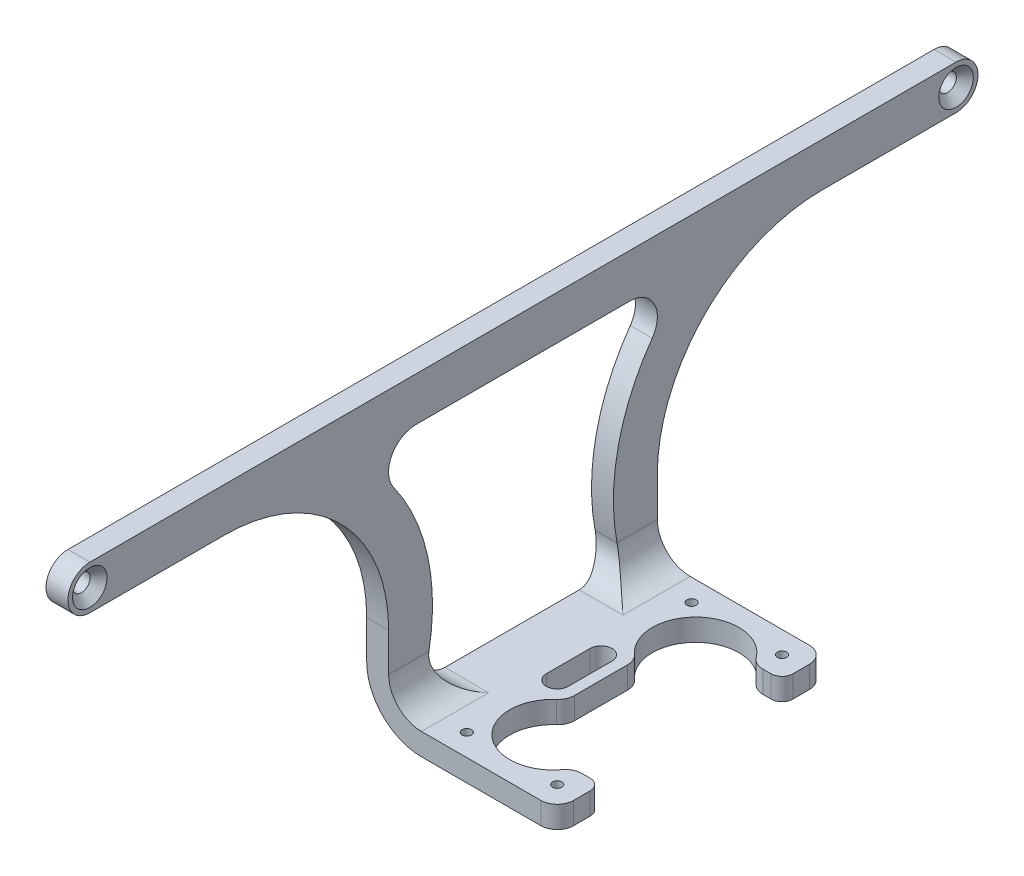
SolidWorks part; units mm, degrees
material "ABS"
ref_plane "Plan de face" through (0, 0, 0) normal (0, 0, 1) x (1, 0, 0)
ref_plane "Plan de dessus" through (0, 0, 0) normal (0, 1, 0) x (1, 0, 0)
ref_plane "Plan de droite" through (0, 0, 0) normal (1, 0, 0) x (0, 0, -1)
sketch "Esquisse1" plane through (0, 0, 0) normal (0, 0, 1) x (1, 0, 0)
  line L0 (0, 0) -> (-25, 0)
  line L1 (-35, 10) -> (-35, 55)
  line L2 (0, 4) -> (-25, 4)
  line L3 (-31, 10) -> (-31, 55)
  line L4 (0, 0) -> (0, 4)
  line L5 (-35, 55) -> (-31, 55)
  arc A2 (-25, 0) -> (-35, 10) centre (-25, 10) cw
  arc A3 (-25, 4) -> (-31, 10) centre (-25, 10) cw
  dimension "D1" = 10
  dimension "D3" = 55
  dimension "D4" = 25
  dimension "D2" = 4
extrude "Boss.-Extru.1" add sketch "Esquisse1" along normal blind 166
hole_wizard "Fraisage pour vis à tête fraisée M31" positions "Esquisse2" profile "Esquisse3" countersink size "M3" standard "ISO" end condition up to next
sketch "Esquisse2" plane through (-31, 0, 0) normal (-1, 0, 0) x (0, 0, 1)
  line L0 (0, 55) -> (0, 10) construction
  line L1 (166, 55) -> (0, 55) construction
  point P0 (4, 51)
  point P2 (162, 51)
  dimension "D1" = 158
  dimension "D2" = 4
  dimension "D3" = 4
sketch "Esquisse3" plane through (-31, 51, 4) normal (0, 1, 0) x (0, 0, -1)
  line L0 (0, 0) -> (0, 4)
  line L1 (0, 4) -> (1.6, 4)
  line L2 (1.6, 4) -> (1.6, 1.55)
  line L3 (1.6, 1.55) -> (3.15, 0)
  line L5 (3.15, 0) -> (0, 0)
  line L6 (-1.6, 1.55) -> (-3.15, 0) construction
  line L11 (0, -6.35) -> (0, 107.95) construction
  dimension "Diamètre du perçage jusqu'au prochain" = 3.2
  dimension "Profondeur du perçage jusqu'au prochain" = 4
  dimension "Diamètre du fraisage entrant" = 6.3
  dimension "Angle du fraisage entrant" = 90
hole_wizard "Dégagement M1.61" positions "Esquisse4" profile "Esquisse5" hole size "M1.6" standard "ISO" end condition up to next
sketch "Esquisse4" plane through (0, 0, 0) normal (0, -1, 0) x (-1, 0, 0)
  line L1 (20.75, -62.5) -> (4.25, -62.5)
  line L2 (20.75, -62.5) -> (20.75, -103.5)
  line L3 (20.75, -103.5) -> (4.25, -103.5)
  line L4 (4.25, -62.5) -> (4.25, -103.5)
  line L5 (20.75, -62.5) -> (4.25, -103.5) construction
  line L6 (20.75, -103.5) -> (4.25, -62.5) construction
  line L7 (25, 0) -> (0, -166) construction
  point P0 (20.75, -62.5)
  point P2 (20.75, -103.5)
  point P4 (4.25, -103.5)
  point P6 (4.25, -62.5)
  point P60 (12.5, -83)
  point P61 (12.5, -83)
  dimension "D1" = 41
  dimension "D2" = 16.5
sketch "Esquisse5" plane through (-20.75, 0, 62.5) normal (1, 0, 0) x (0, 0, -1)
  line L0 (0, 0) -> (0, 4)
  line L1 (0, 4) -> (0.85, 4)
  line L2 (0.85, 4) -> (0.85, 0)
  line L5 (0.85, 0) -> (0, 0)
  line L11 (0, -6.35) -> (0, 107.95) construction
  dimension "Diamètre du perçage jusqu'au prochain" = 1.7
  dimension "Profondeur du perçage jusqu'au prochain" = 4
sketch "Esquisse6" plane through (0, 0, 0) normal (0, -1, 0) x (1, 0, 0)
  line L1 (-35, 58.5) -> (-3.25, 58.5)
  line L2 (-0.25, 61.5) -> (-0.25, 64.5)
  line L3 (-3.25, 107.5) -> (-35, 107.5)
  line L5 (-35, 0) -> (0, 0)
  line L6 (0, 0) -> (0, 166)
  line L7 (0, 166) -> (-35, 166)
  line L8 (-0.25, 101.5) -> (-0.25, 104.5)
  line L9 (-3.7501, 66.5) -> (-2.25, 66.5)
  line L10 (-16.75, 78.1393) -> (-16.75, 87.8607)
  line L11 (-3.7501, 99.5) -> (-2.25, 99.5)
  line L13 (-19.25, 83) -> (0, 83) construction
  line L14 (-4.25, 103.5) -> (-12.5, 96) construction
  line L15 (-12.5, 96) -> (-20.75, 103.5) construction
  line L17 (0, 166) -> (0, 0) construction
  line L18 (-35, 166) -> (-35, 0) construction
  line L19 (-35, 107.5) -> (-35, 166)
  line L20 (-35, 58.5) -> (-35, 0)
  line L21 (-20.75, 87) -> (-20.75, 79) construction
  line L22 (-18.75, 87) -> (-18.75, 79)
  line L23 (-22.75, 87) -> (-22.75, 79)
  circle A0 centre (-4.25, 62.5) radius 0.85 construction
  circle A1 centre (-4.25, 103.5) radius 0.85 construction
  arc A2 (-0.25, 104.5) -> (-3.25, 107.5) centre (-3.25, 104.5) ccw
  arc A3 (-3.25, 58.5) -> (-0.25, 61.5) centre (-3.25, 61.5) ccw
  circle A6 centre (-20.75, 62.5) radius 0.85 construction
  circle A7 centre (-20.75, 103.5) radius 0.85 construction
  arc A12 (-6.1584, 100.711) -> (-17.7546, 90.1009) centre (-12.5, 96) ccw
  arc A13 (-17.7546, 75.8991) -> (-6.1584, 65.289) centre (-12.5, 70) ccw
  arc A14 (-6.1584, 65.289) -> (-3.7501, 66.5) centre (-3.7501, 63.5) cw
  arc A15 (-17.7546, 75.8991) -> (-16.75, 78.1393) centre (-19.75, 78.1393) ccw
  arc A16 (-3.7501, 99.5) -> (-6.1584, 100.711) centre (-3.7501, 102.5) cw
  arc A17 (-16.75, 87.8607) -> (-17.7546, 90.1009) centre (-19.75, 87.8607) ccw
  arc A18 (-2.25, 66.5) -> (-0.25, 64.5) centre (-2.25, 64.5) cw
  arc A19 (-2.25, 99.5) -> (-0.25, 101.5) centre (-2.25, 101.5) ccw
  arc A20 (-18.75, 87) -> (-22.75, 87) centre (-20.75, 87) ccw
  arc A21 (-22.75, 79) -> (-18.75, 79) centre (-20.75, 79) ccw
  point P8 (-20.75, 83)
  point P40 (-0.25, 99.5)
  dimension "D1" = 4
  dimension "D2" = 4
  dimension "D5" = 4
  dimension "D6" = 3
  dimension "D7" = 8
  dimension "D12" = 3
  dimension "D11" = 15.8
  dimension "D3" = 2
  dimension "D4" = 4
  dimension "D8" = 4
  dimension "D9" = 4
  dimension "D10" = 4
  dimension "D13" = 26
  dimension "D14" = 4
extrude "Enlèv. mat.-Extru.1" cut sketch "Esquisse6" against normal up to surface (4 mm away) up to face at (-19.9, 4, 62.5)
sketch "Esquisse7" plane through (-31, 0, 0) normal (1, 0, 0) x (0, 0, -1)
  line L0 (-166, 55) -> (0, 55) construction
  line L24 (0, 51) -> (0, 4)
  line L25 (-166, 51) -> (-166, 55)
  line L26 (-166, 55) -> (-162, 55)
  line L27 (-4, 55) -> (0, 55)
  line L28 (0, 55) -> (0, 51)
  line L29 (-162, 47) -> (-137.5, 47)
  line L30 (-107.5, 17) -> (-107.5, 4)
  line L31 (-4, 47) -> (-28.5, 47)
  line L32 (-58.5, 17) -> (-58.5, 4)
  line L33 (0, 4) -> (-58.5, 4)
  line L34 (-107.5, 4) -> (-166, 4)
  line L35 (-166, 4) -> (-166, 51)
  line L39 (-102.5143, 47) -> (-63.4857, 47)
  line L40 (-70.7493, 4) -> (-95.2507, 4)
  line L41 (-107.5, 4) -> (-58.5, 4) construction
  circle A8 centre (-162, 51) radius 4
  circle A15 centre (-4, 51) radius 4
  arc A16 (-28.5, 47) -> (-58.5, 17) centre (-28.5, 17) ccw
  arc A17 (-137.5, 47) -> (-107.5, 17) centre (-137.5, 17) cw
  arc A18 (-100.1634, 9.9302) -> (-106.5824, 39.093) centre (-137.5, 17) ccw
  arc A19 (-59.4176, 39.093) -> (-65.8366, 9.9302) centre (-28.5, 17) ccw
  arc A20 (-95.2507, 4) -> (-100.1634, 9.9302) centre (-95.2507, 9) cw
  arc A21 (-70.7493, 4) -> (-65.8366, 9.9302) centre (-70.7493, 9) ccw
  arc A22 (-63.4857, 47) -> (-59.4176, 39.093) centre (-63.4857, 42) cw
  arc A23 (-102.5143, 47) -> (-106.5824, 39.093) centre (-102.5143, 42) ccw
  point P20 (-107.5, 47)
  point P38 (-28.5, 45)
  point P41 (-137.5, 45)
  line M10 (0, 10) -> (0, 55)
  line M12 (0, 55) -> (-166, 55)
  line M14 (-166, 55) -> (-166, 10)
  line M15 (-166, 10) -> (0, 10)
  dimension "D1" = 30
  dimension "D2" = 5
extrude "Enlèv. mat.-Extru.2" cut sketch "Esquisse7" against normal through all and the other way through all contours A23 A18 A20 A21 A19 A22 M12 M15 | A17 L29 A8 M14 M15 | L31 A16 A15 M15 M10 | A15 M10 M12 | A8 M12 M14 | A17 L35 L34 L30 M15 | A16 L32 L33 L24 M15 | L40 A21 A19 A18 A20 M15
